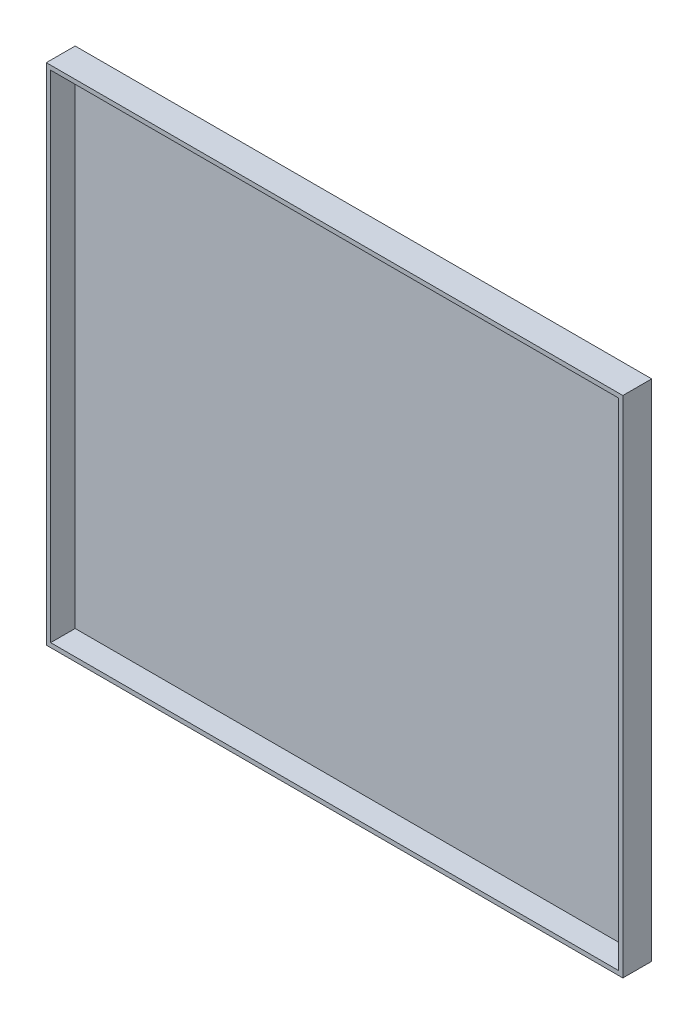
SolidWorks part; units mm, degrees
material "玻璃"
ref_plane "前视基准面" through (0, 0, 0) normal (0, 0, 1) x (1, 0, 0)
ref_plane "上视基准面" through (0, 0, 0) normal (0, 1, 0) x (1, 0, 0)
ref_plane "右视基准面" through (0, 0, 0) normal (1, 0, 0) x (0, 0, -1)
sketch "草图1" plane through (0, 0, 0) normal (0, 0, 1) x (1, 0, 0)
  line L1 (-200, 175) -> (200, 175)
  line L2 (-200, 175) -> (-200, -175)
  line L3 (-200, -175) -> (200, -175)
  line L4 (200, 175) -> (200, -175)
  line L5 (-200, 175) -> (200, -175) construction
  line L6 (-200, -175) -> (200, 175) construction
  point P0 (0, 0)
  dimension "D1" = 400
  dimension "D2" = 350
extrude "凸台-拉伸1" add sketch "草图1" along normal blind 20
shell "抽壳1" thickness 3
